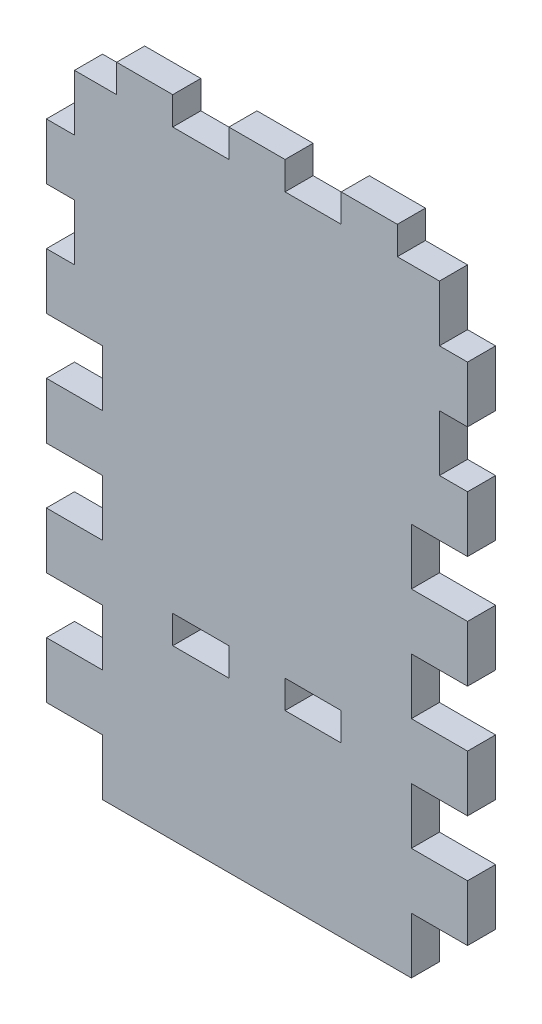
SolidWorks part; units mm, degrees
material "Pine"
ref_plane "Front Plane" through (0, 0, 0) normal (0, 0, 1) x (1, 0, 0)
ref_plane "Top Plane" through (0, 0, 0) normal (0, 1, 0) x (1, 0, 0)
ref_plane "Right Plane" through (0, 0, 0) normal (1, 0, 0) x (0, 0, -1)
sketch "Sketch1" plane through (0, 0, 0) normal (0, 0, 1) x (1, 0, 0)
  line L1 (0, 0) -> (95.25, 0)
  line L2 (0, 0) -> (0, 177.8)
  line L3 (0, 177.8) -> (95.25, 177.8)
  line L4 (95.25, 0) -> (95.25, 177.8)
  dimension "D1" = 95.25
  dimension "D2" = 177.8
extrude "Boss-Extrude1" add sketch "Sketch1" along normal blind 6.35 contours L3 L4 L1 L2
sketch "Sketch2" plane through (0, 0, 6.35) normal (0, 0, 1) x (1, 0, 0)
  line L0 (0, 0) -> (0, 177.8) construction
  line L1 (0, 12.7) -> (12.7, 12.7)
  line L2 (0, 12.7) -> (0, 0)
  line L3 (0, 0) -> (12.7, 0)
  line L4 (12.7, 12.7) -> (12.7, 0)
  line L5 (0, 0) -> (95.25, 0) construction
  line L6 (95.25, 0) -> (95.25, 177.8) construction
  line L7 (95.25, 12.7) -> (82.55, 12.7)
  line L8 (95.25, 12.7) -> (95.25, 0)
  line L9 (95.25, 0) -> (82.55, 0)
  line L10 (82.55, 12.7) -> (82.55, 0)
  dimension "D1" = 12.7
  dimension "D2" = 12.7
extrude "Cut-Extrude1" cut sketch "Sketch2" against normal through all
pattern_linear "LPattern1" count 4 spacing 25.4 along (0, 1, 0) of "Cut-Extrude1"
sketch "Sketch3" plane through (0, 0, 6.35) normal (0, 0, 1) x (1, 0, 0)
  line L0 (47.625, 0) -> (47.625, 41.275) construction
  line L1 (28.575, 44.45) -> (41.275, 44.45)
  line L2 (28.575, 44.45) -> (28.575, 38.1)
  line L3 (28.575, 38.1) -> (41.275, 38.1)
  line L4 (41.275, 44.45) -> (41.275, 38.1)
  line L5 (53.975, 44.45) -> (66.675, 44.45)
  line L6 (53.975, 44.45) -> (53.975, 38.1)
  line L7 (53.975, 38.1) -> (66.675, 38.1)
  line L8 (66.675, 44.45) -> (66.675, 38.1)
  line L9 (12.7, 0) -> (82.55, 0) construction
  line L10 (41.275, 41.275) -> (53.975, 41.275) construction
  dimension "D1" = 12.7
  dimension "D2" = 6.35
  dimension "D3" = 38.1
extrude "Cut-Extrude2" cut sketch "Sketch3" against normal through all
sketch "Sketch4" plane through (0, 0, 6.35) normal (0, 0, 1) x (1, 0, 0)
  line L0 (44.45, 163.25) -> (44.45, 99.25) construction
  line L1 (0, 88.9) -> (0, 177.8) construction
  line L2 (12.7, 0) -> (82.55, 0) construction
  line L4 (44.45, 163.25) -> (57.15, 163.25) construction
  line L5 (44.45, 163.25) -> (44.45, 99.25) construction
  line L6 (44.45, 99.25) -> (57.15, 99.25) construction
  line L7 (57.15, 163.25) -> (57.15, 99.25) construction
  circle A0 centre (44.45, 163.25) radius 1.75
  circle A1 centre (44.45, 99.25) radius 1.75
  circle A2 centre (57.15, 163.25) radius 1.75
  circle A3 centre (57.15, 99.25) radius 1.75
  dimension "D4" = 3.5
  dimension "D1" = 44.45
  dimension "D2" = 64
  dimension "D3" = 99.25
  dimension "D5" = 12.7
sketch "Sketch5" plane through (0, 0, 6.35) normal (0, 0, 1) x (1, 0, 0)
  line L0 (0, 88.9) -> (0, 177.8) construction
  line L1 (0, 101.6) -> (6.35, 101.6)
  line L2 (0, 101.6) -> (0, 114.3)
  line L3 (0, 114.3) -> (6.35, 114.3)
  line L4 (6.35, 101.6) -> (6.35, 114.3)
  line L5 (95.25, 88.9) -> (95.25, 177.8) construction
  line L6 (95.25, 114.3) -> (88.9, 114.3)
  line L7 (95.25, 114.3) -> (95.25, 101.6)
  line L8 (95.25, 101.6) -> (88.9, 101.6)
  line L9 (88.9, 114.3) -> (88.9, 101.6)
  line L10 (12.7, 76.2) -> (12.7, 88.9) construction
  line L11 (12.7, 88.9) -> (0, 88.9) construction
  dimension "D1" = 12.7
  dimension "D2" = 6.35
extrude "Cut-Extrude4" cut sketch "Sketch5" against normal through all
pattern_linear "LPattern2" count 4 spacing 25.4 along (0, 1, 0) of "Cut-Extrude4"
sketch "Sketch6" plane through (0, 0, 6.35) normal (0, 0, 1) x (1, 0, 0)
  line L1 (0, 177.8) -> (95.25, 177.8)
  line L2 (0, 177.8) -> (0, 139.7)
  line L3 (0, 139.7) -> (95.25, 139.7)
  line L4 (95.25, 177.8) -> (95.25, 139.7)
extrude "Cut-Extrude5" cut sketch "Sketch6" against normal through all
sketch "Sketch7" plane through (0, 139.7, 0) normal (0, 1, 0) x (1, 0, 0)
  line L0 (6.35, 0) -> (88.9, 0) construction
  line L1 (41.275, 0) -> (53.975, 0)
  line L2 (41.275, 0) -> (41.275, -6.35)
  line L3 (41.275, -6.35) -> (53.975, -6.35)
  line L4 (53.975, 0) -> (53.975, -6.35)
  line L5 (6.35, -6.35) -> (88.9, -6.35) construction
  point P8 (47.625, -6.35)
  dimension "D1" = 12.7
extrude "Boss-Extrude2" add sketch "Sketch7" along normal blind 6.35
pattern_linear "LPattern3" count 2 spacing 25.4 along (1, 0, 0) count 2 spacing 25.4 along (-1, 0, 0) of "Boss-Extrude2"
